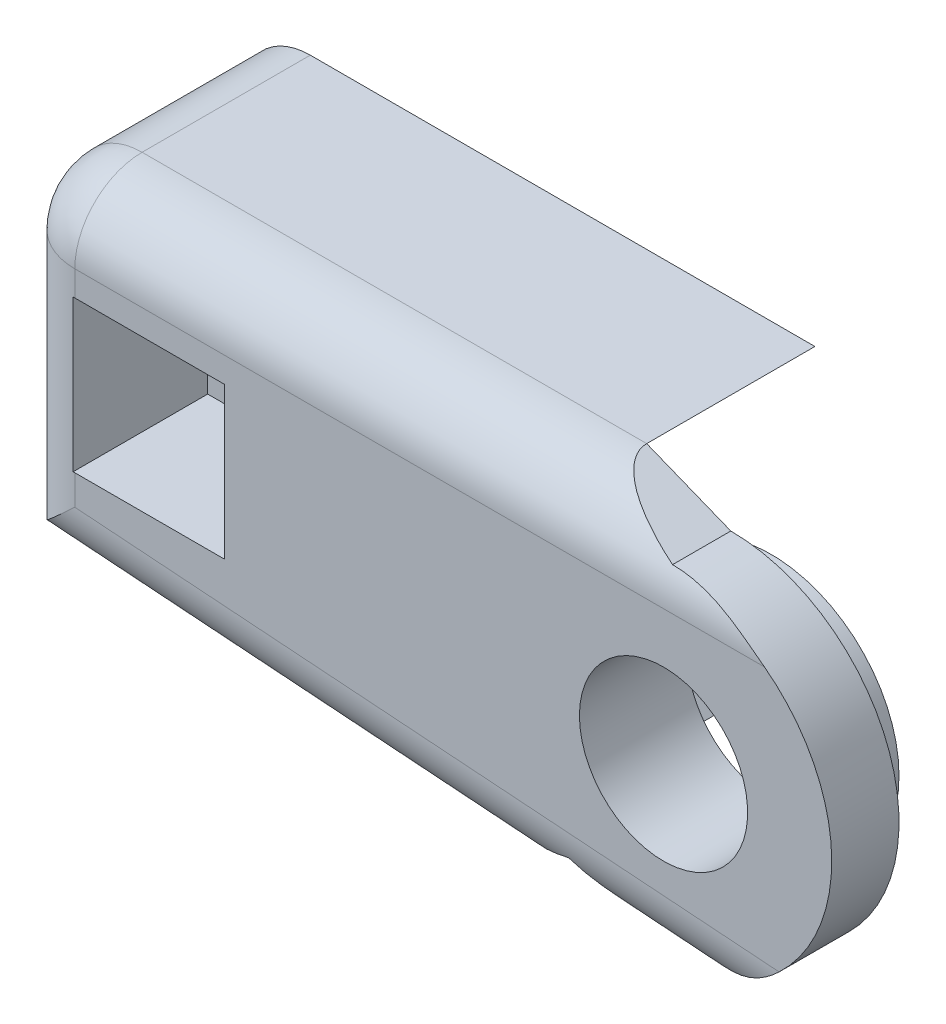
SolidWorks part; units mm, degrees
ref_plane "Front Plane" through (0, 0, 0) normal (0, 0, 1) x (1, 0, 0)
ref_plane "Top Plane" through (0, 0, 0) normal (0, 1, 0) x (1, 0, 0)
ref_plane "Right Plane" through (0, 0, 0) normal (1, 0, 0) x (0, 0, -1)
sketch "Sketch2" plane through (0, 0, 0) normal (0, 0, 1) x (1, 0, 0)
  line L0 (0, 5) -> (-2.5, 6)
  line L1 (-2.5, 6) -> (-19.5, 6)
  line L2 (-19.5, 6) -> (-19.5, -4)
  line L3 (-19.5, -4) -> (-5.5, -5)
  line L4 (-5.5, -5) -> (-3, -4)
  arc A1 (-3, -4) -> (0, 5) centre (0, 0) ccw
  dimension "D1" = 10
  dimension "D3" = 10
  dimension "D4" = 6
  dimension "D5" = 11
  dimension "D6" = 2.5
  dimension "D7" = 2.5
  dimension "D8" = 14
extrude "Boss-Extrude1" add sketch "Sketch2" along normal blind 2 contours A1 L0 L1 L2 L3 L4
sketch "Sketch3" plane through (0, 0, 0) normal (0, 0, -1) x (-1, 0, 0)
  circle A1 centre (0, 0) radius 2.5
  dimension "D1" = 5
extrude "Cut-Extrude1" cut sketch "Sketch3" against normal blind 2
sketch "Sketch4" plane through (0, 0, 2) normal (0, 0, 1) x (1, 0, 0)
  line L0 (-19.5, -4) -> (-19.5, 6)
  line L1 (-19.5, 6) -> (-2.5, 6)
  line L2 (-2.5, 6) -> (-5.3494, 4.5)
  line L3 (-5.3494, 4.5) -> (-18.3, 4.5)
  line L4 (-18.3, 4.5) -> (-18.3, -2.5819)
  line L5 (-19.5, -4) -> (-5.5, -5) construction
  line L6 (-19.2926, -4.0148) -> (-19.5, -4)
  line L7 (-19.2926, -4.0148) -> (-5.5, -5)
  line L8 (-5.5, -5) -> (-6.7591, -3.4062)
  line L9 (-6.7591, -3.4062) -> (-18.3, -2.5819)
  dimension "D1" = 1.5
  dimension "D2" = 1.2
  dimension "D3" = 1.5
extrude "Boss-Extrude2" add sketch "Sketch4" along normal blind 5
ref_plane "Plane1" through (0, 0, 7) normal (0, 0, 1) x (1, 0, 0)
sketch "Sketch7" plane through (0, 4.5, 0) normal (0, -1, 0) x (1, 0, 0)
  line L0 (-18.3, 7) -> (-5.3494, 7) construction
  circle A0 centre (-10.3494, 7) radius 0.5
  point P2 (0, 0)
  point P3 (-6.211, 7)
  point P6 (0, 0)
  dimension "D1" = 5
fillet "Fillet2" radius 2 4 edges at (-19.5, 1, 0) (-19.5, 6, 3.5) (-12.5, -4.5, 0) (-11, 6, 0)
sketch "Sketch8" plane through (0, 0, 2) normal (0, 0, 1) x (1, 0, 0)
  circle A1 centre (0, 0) radius 3.8
  circle A2 centre (0, 0) radius 2.5
extrude "Boss-Extrude3" add sketch "Sketch8" along normal blind 1.2
sketch "Sketch11" plane through (0, 0, 7) normal (0, 0, 1) x (1, 0, 0)
  line L0 (-10.3494, 4.5) -> (-2.1686, -4.2175) construction
extrude "Cut-Extrude3" cut sketch "Sketch7" along direction (0.6843, -0.7292, 0) on the side against the normal blind 2 contours A0
sketch "Sketch15" plane through (-0.2764, -3.8693, 0) normal (0.0712, 0.9975, 0) x (0.9975, -0.0712, 0)
  line L0 (-6.4992, -7) -> (-18.0695, -7) construction
  circle A0 centre (-9.5378, -7) radius 0.5
sketch "Sketch17" plane through (0, 0, 7) normal (0, 0, 1) x (1, 0, 0)
  line L0 (-9.7899, -3.1898) -> (-2.3462, 3.8366) construction
  line L1 (-9.2912, -3.2254) -> (-10.2886, -3.1541) construction
extrude "Cut-Extrude5" cut sketch "Sketch15" along direction (0.7272, 0.6864, 0) on the side against the normal blind 3
sketch "Sketch18" plane through (0, 0, 2) normal (0, 0, 1) x (1, 0, 0)
  line L0 (-18.3, 4.5) -> (-11.3, 4.5)
  line L1 (-18.3, 4.5) -> (-18.3, -3.0738)
  line L2 (-11.3, 4.5) -> (-11.3, -3.0738)
  line L3 (-18.3, -3.0738) -> (-11.3, -3.0738)
  line L4 (-18.3, -2.5819) -> (-18.3, 4.5) construction
  dimension "D1" = 0
  dimension "D3" = 7
extrude "Boss-Extrude4" add sketch "Sketch18" along normal blind 5
sketch "Sketch19" plane through (0, 0, 7) normal (0, 0, 1) x (1, 0, 0)
  line L0 (-11.3, -3.0738) -> (-11.3, 4.5) construction
  circle A0 centre (-15.3, 1) radius 1
  point P4 (0, 0)
  point P6 (-14.6141, 2.1847)
  dimension "D1" = 4
extrude "Cut-Extrude6" cut sketch "Sketch19" against normal blind 3
sketch "Sketch20" plane through (0, 0, 4) normal (0, 0, 1) x (1, 0, 0)
  line L1 (-17.55, 3.25) -> (-13.05, 3.25)
  line L2 (-17.55, 3.25) -> (-17.55, -1.25)
  line L3 (-17.55, -1.25) -> (-13.05, -1.25)
  line L4 (-13.05, 3.25) -> (-13.05, -1.25)
  line L5 (-17.55, 3.25) -> (-13.05, -1.25) construction
  line L6 (-17.55, -1.25) -> (-13.05, 3.25) construction
  point P0 (-15.3, 1)
  dimension "D1" = 4.5
  dimension "D2" = 4.5
extrude "Cut-Extrude7" cut sketch "Sketch20" against normal blind 5
mirror "Mirror1" about plane through (0, 0, 7) normal (0, 0, 1) of bodies 118
split "Split1" trim tools "Plane1" bodies to split 119 resulting bodies 120 121
delete or keep bodies "Body-Delete/Keep 1" type delete bodies bodies 121
